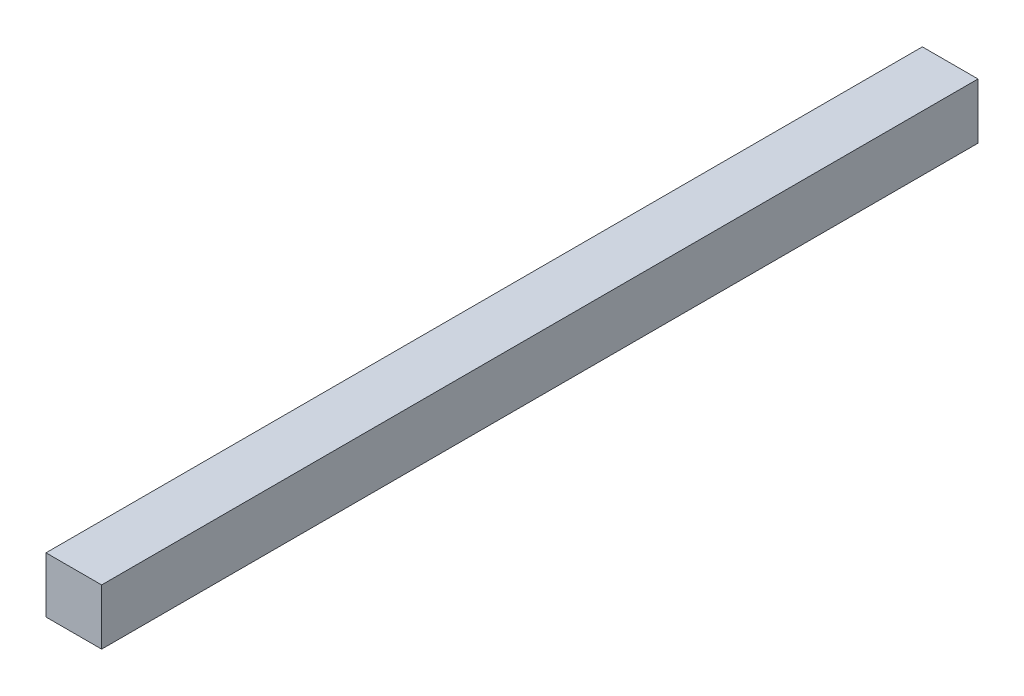
SolidWorks part; units mm, degrees
ref_plane "Płaszczyzna przednia" through (0, 0, 0) normal (0, 0, 1) x (1, 0, 0)
ref_plane "Płaszczyzna górna" through (0, 0, 0) normal (0, 1, 0) x (1, 0, 0)
ref_plane "Płaszczyzna prawa" through (0, 0, 0) normal (1, 0, 0) x (0, 0, -1)
sketch "Szkic1" plane through (0, 0, 0) normal (0, 0, 1) x (1, 0, 0)
  line L1 (0, 0) -> (20, 0)
  line L2 (0, 0) -> (0, 20)
  line L3 (0, 20) -> (20, 20)
  line L4 (20, 0) -> (20, 20)
  dimension "D1" = 20
  dimension "D2" = 20
extrude "Dodanie-wyciągnięcie1" add sketch "Szkic1" against normal blind 315
